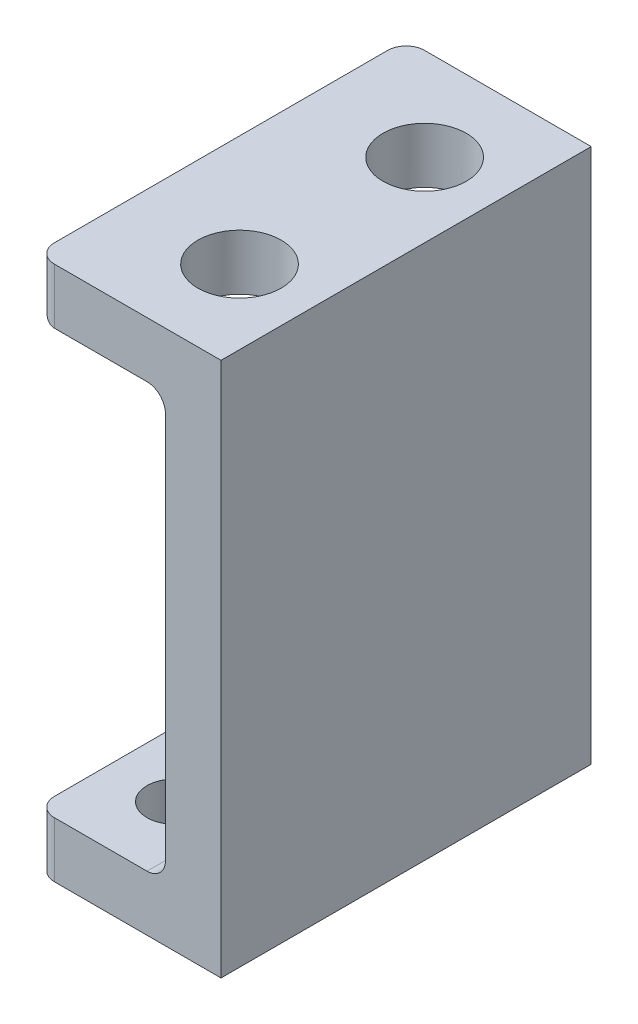
SolidWorks part; units mm, degrees
ref_plane "Front Plane" through (0, 0, 0) normal (0, 0, 1) x (1, 0, 0)
ref_plane "Top Plane" through (0, 0, 0) normal (0, 1, 0) x (1, 0, 0)
ref_plane "Right Plane" through (0, 0, 0) normal (1, 0, 0) x (0, 0, -1)
sketch "Sketch1" plane through (0, 0, 0) normal (0, 0, 1) x (1, 0, 0)
  line L0 (0, -10.5819) -> (0, 12.3181)
  line L1 (0, 12.3181) -> (-7, 12.3181)
  line L2 (-7, 12.3181) -> (-7, 15.3181)
  line L3 (-7, 15.3181) -> (3, 15.3181)
  line L4 (3, 15.3181) -> (3, -13.5819)
  line L5 (3, -13.5819) -> (-7, -13.5819)
  line L6 (-7, -13.5819) -> (-7, -10.5819)
  line L7 (-7, -10.5819) -> (0, -10.5819)
  dimension "D1" = 28.9
  dimension "D2" = 3
  dimension "D3" = 3
  dimension "D4" = 3
  dimension "D5" = 10
  dimension "D6" = 10
extrude "Boss-Extrude1" add sketch "Sketch1" along normal blind 20
sketch "Sketch2" plane through (0, 15.3181, 0) normal (0, 1, 0) x (1, 0, 0)
  line L0 (3, -20) -> (3, 0) construction
  line L1 (-1, -5) -> (-1, -15) construction
  line L2 (-7, -20) -> (-7, 0) construction
  circle A0 centre (-1, -5) radius 2.25
  circle A1 centre (-1, -15) radius 2.25
  point P6 (-7, -10)
  point P7 (-1, -10)
  dimension "D1" = 4.5
  dimension "D2" = 4.5
  dimension "D3" = 4
  dimension "D4" = 10
extrude "Cut-Extrude1" cut sketch "Sketch2" against normal blind 20
sketch "Sketch3" plane through (0, -10.5819, 0) normal (0, 1, 0) x (1, 0, 0)
  line L0 (-7, -20) -> (-7, 0) construction
  line L1 (-3.5, -4) -> (-3.5, -10) construction
  line L2 (-3.5, -10) -> (-3.5, -16) construction
  line L3 (0, -16) -> (-7, -16) construction
  line L4 (0, -20) -> (0, 0) construction
  circle A0 centre (-3.5, -4) radius 1.5
  circle A1 centre (-3.5, -10) radius 1.5
  circle A2 centre (-3.5, -16) radius 1.5
  point P9 (-7, -10)
  point P12 (-3.5, -16)
  dimension "D1" = 3
  dimension "D2" = 3
  dimension "D3" = 3
  dimension "D4" = 6
extrude "Cut-Extrude2" cut sketch "Sketch3" against normal blind 20
fillet "Fillet1" radius 1 6 edges at (0, -10.5819, 10) (-7, -12.0819, 0) (-7, -12.0819, 20) (-7, 12.3181, 10) (-7, 13.8181, 0) (-7, 13.8181, 20)
fillet "Fillet2" radius 1 3 edges at (0, 12.3181, 18.5078) (0, 12.3181, 1.4922) (0, 12.3181, 10)
